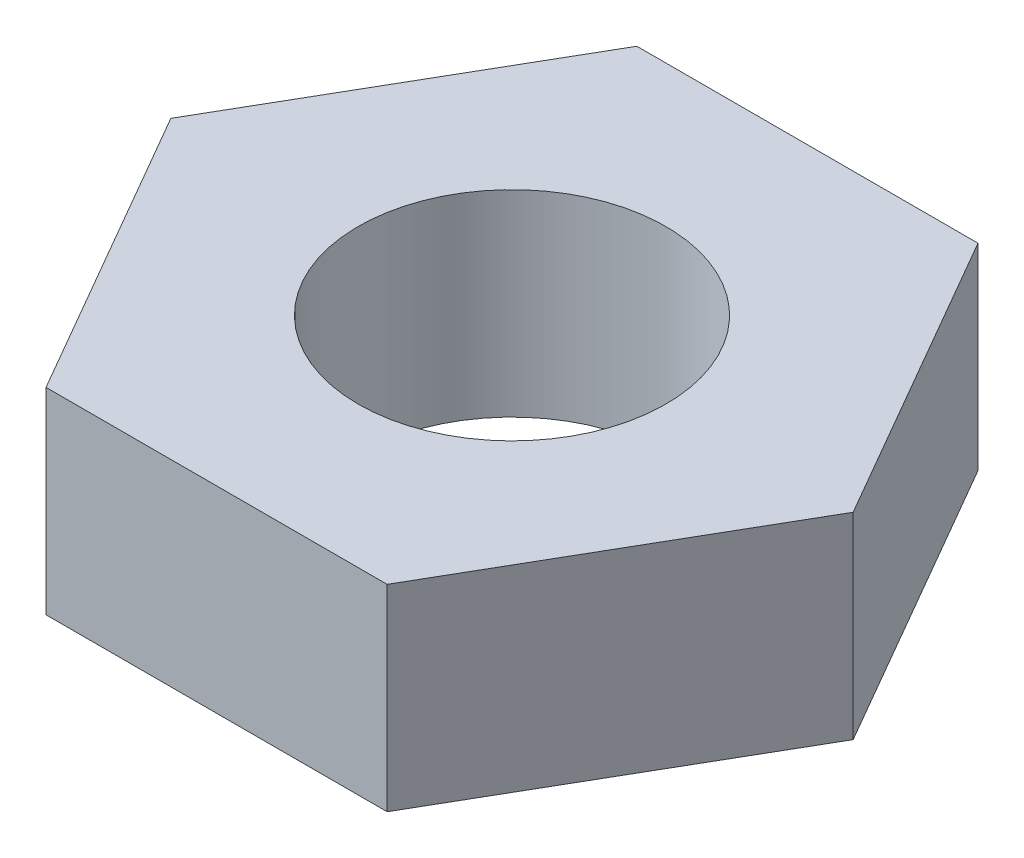
SolidWorks part; units mm, degrees
material "Brass"
ref_plane "Front Plane" through (0, 0, 0) normal (0, 0, 1) x (1, 0, 0)
ref_plane "Top Plane" through (0, 0, 0) normal (0, 1, 0) x (1, 0, 0)
ref_plane "Right Plane" through (0, 0, 0) normal (1, 0, 0) x (0, 0, -1)
sketch "Sketch1" plane through (0, 0, 0) normal (0, 1, 0) x (1, 0, 0)
  line L1 (5.4993, 9.525) -> (-5.4993, 9.525)
  line L2 (-5.4993, 9.525) -> (-10.9985, 0)
  line L3 (-10.9985, 0) -> (-5.4993, -9.525)
  line L4 (-5.4993, -9.525) -> (5.4993, -9.525)
  line L5 (5.4993, -9.525) -> (10.9985, 0)
  line L6 (10.9985, 0) -> (5.4993, 9.525)
  circle A0 centre (0, 0) radius 9.525 construction
  dimension "D1" = 19.05
extrude "Boss-Extrude1" add sketch "Sketch1" along normal blind 6.35
sketch "Sketch4" plane through (0, 6.35, 0) normal (0, 1, 0) x (1, 0, 0)
  point P0 (0, 0)
hole_wizard "7/16-20 Tapped Hole1" positions "Sketch5" profile "Sketch7" tap size "7/16-20" standard "ANSI Inch" end condition through all
sketch "Sketch5" plane through (0, 6.35, 0) normal (0, 1, 0) x (1, 0, 0)
  point P0 (0, 0)
sketch "Sketch7" plane through (0, 6.35, 0) normal (1, 0, 0) x (0, 0, 1)
  line L0 (0, 0) -> (0, 6.35)
  line L1 (0, 6.35) -> (4.9606, 6.35)
  line L2 (4.9606, 6.35) -> (4.9606, 0)
  line L5 (4.9606, 0) -> (0, 0)
  line L11 (0, -6.35) -> (0, 107.95) construction
  dimension "Thru Tap Drill Dia." = 9.9212
  dimension "Thru Tap Drill Depth" = 6.35
cosmetic thread "Hole Thread1" parameters "D2"=11.1125
